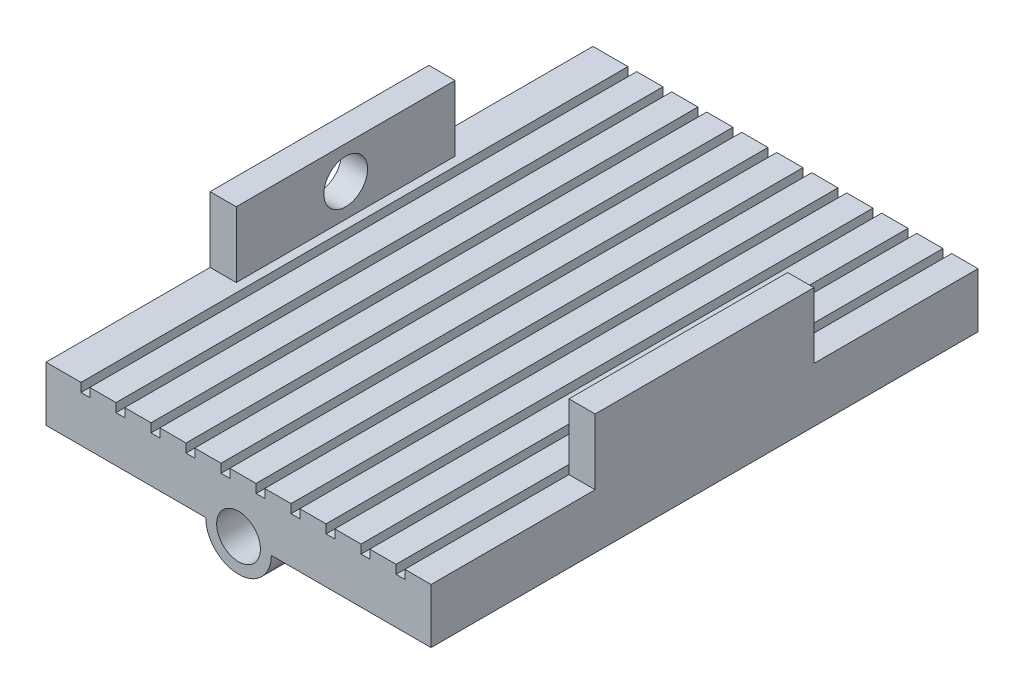
SolidWorks part; units mm, degrees
ref_plane "Front Plane" through (0, 0, 0) normal (0, 0, 1) x (1, 0, 0)
ref_plane "Top Plane" through (0, 0, 0) normal (0, 1, 0) x (1, 0, 0)
ref_plane "Right Plane" through (0, 0, 0) normal (1, 0, 0) x (0, 0, -1)
sketch "Sketch1" plane through (0, 0, 0) normal (0, 0, 1) x (1, 0, 0)
  line L0 (15, 0) -> (88, 0)
  line L1 (88, 0) -> (88, 25)
  line L2 (88, 25) -> (-88, 25)
  line L3 (-88, 25) -> (-88, 0)
  line L4 (-88, 0) -> (-15, 0)
  arc A0 (-15, 0) -> (15, 0) centre (0, 0) ccw
  point P10 (0, 25)
  dimension "D1" = 15
  dimension "D2" = 25
  dimension "D3" = 176
extrude "Boss-Extrude1" add sketch "Sketch1" along normal blind 250
sketch "Sketch3" plane through (0, 0, 250) normal (0, 0, 1) x (1, 0, 0)
  circle A0 centre (0, 0) radius 10
extrude "Cut-Extrude1" cut sketch "Sketch3" against normal through all
sketch "Sketch4" plane through (0, 0, 250) normal (0, 0, 1) x (1, 0, 0)
  line L0 (88, 25) -> (-88, 25) construction
  line L2 (-72, 25) -> (-72, 21)
  line L3 (-72, 21) -> (-68, 21)
  line L4 (-68, 25) -> (-68, 21)
  line L5 (-78.5899, 25) -> (-68, 21) construction
  line L6 (-72, 21) -> (-78.5899, 25) construction
  line L7 (-72, 25) -> (-68, 25)
  line L8 (-88, 25) -> (-88, 0) construction
  point P0 (-78.5899, 25)
  dimension "D1" = 4
  dimension "D2" = 4
  dimension "D3" = 16
extrude "Cut-Extrude2" cut sketch "Sketch4" against normal through all
pattern_linear "LPattern1" count 10 spacing 16 along (1, 0, 0) of "Cut-Extrude2"
sketch "Sketch5" plane through (0, 25, 0) normal (0, 1, 0) x (1, 0, 0)
  line L0 (-88, -250) -> (-88, 0) construction
  line L1 (-88, -75) -> (-76.0216, -75)
  line L2 (-88, -75) -> (-88, -175)
  line L3 (-88, -175) -> (-76.0216, -175)
  line L4 (-76.0216, -75) -> (-76.0216, -175)
  line L5 (-72, 0) -> (-88, 0) construction
  line L6 (-72, -250) -> (-88, -250) construction
  dimension "D1" = 100
  dimension "D2" = 75
  dimension "D3" = 75
extrude "Boss-Extrude2" add sketch "Sketch5" along normal blind 30
ref_plane "Plane1" through (0, 0, 0) normal (-1, 0, 0) x (0, 0, 1)
mirror "Mirror1" about plane through (0, 0, 0) normal (-1, 0, 0) of "Boss-Extrude2"
sketch "Sketch6" plane through (-88, 0, 0) normal (-1, 0, 0) x (0, 0, 1)
  line L0 (75, 55) -> (175, 55) construction
  line L1 (75, 55) -> (75, 25) construction
  circle A0 centre (125, 40) radius 10
  dimension "D1" = 20
  dimension "D2" = 15
  dimension "D3" = 50
extrude "Cut-Extrude3" cut sketch "Sketch6" against normal blind 20
